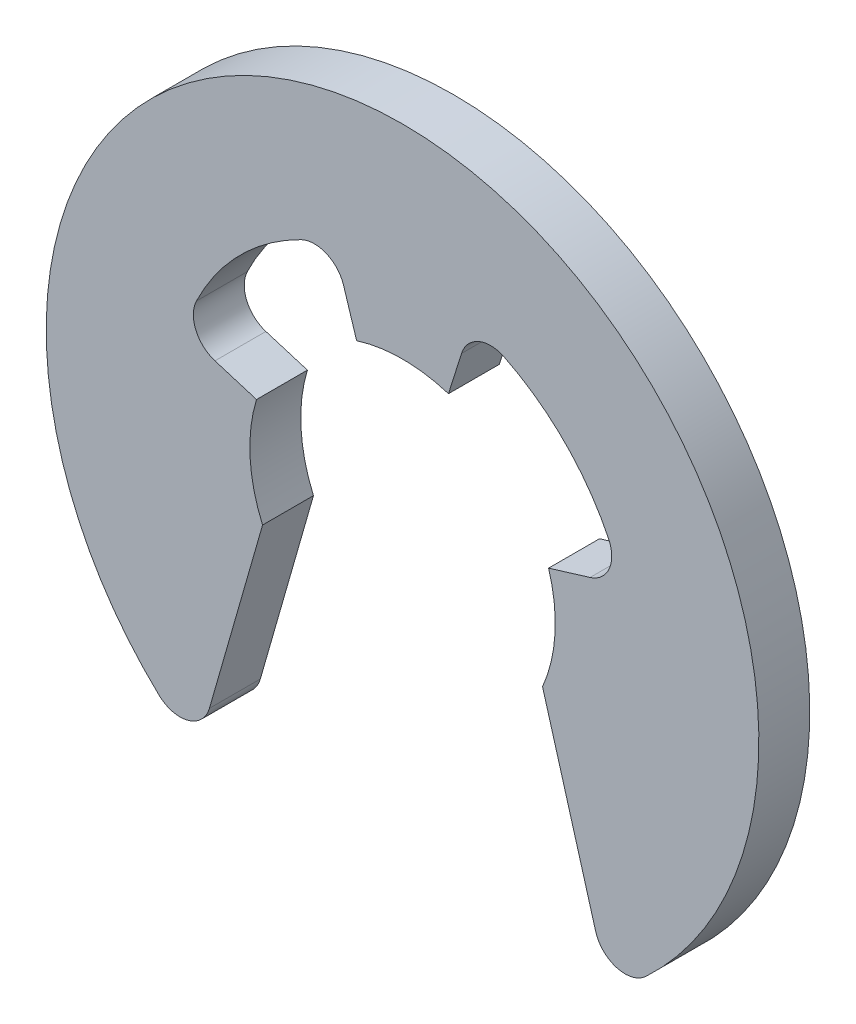
SolidWorks part; units mm, degrees
ref_plane "前视基准面" through (0, 0, 0) normal (0, 0, 1) x (1, 0, 0)
ref_plane "上视基准面" through (0, 0, 0) normal (0, 1, 0) x (1, 0, 0)
ref_plane "右视基准面" through (0, 0, 0) normal (1, 0, 0) x (0, 0, -1)
sketch "草图1" plane through (0, 0, 0) normal (0, 0, 1) x (1, 0, 0)
  line L0 (0, 0) -> (4.4829, 0.3922) construction
  line L1 (-2.193, 0) -> (1.9152, 0) construction
  line L2 (0, -1.8051) -> (0, 1.7867) construction
  line L3 (2.75, -1.199) -> (3.7941, -4.8403)
  line L4 (-2.75, -1.199) -> (-3.7941, -4.8403)
  line L5 (0.9021, 2.8612) -> (1.1588, 3.6752)
  line L6 (-0.9021, 2.8612) -> (-1.1588, 3.6752)
  line L7 (0, 0) -> (0.9021, 2.8612) construction
  line L8 (0.9021, 2.8612) -> (0, 0) construction
  line L9 (0, 0) -> (-0.9021, 2.8612) construction
  line L10 (2.8689, 0.8771) -> (3.6852, 1.1267)
  line L11 (-2.8689, 0.8771) -> (-3.6852, 1.1267)
  line L12 (0, 0) -> (2.8689, 0.8771) construction
  line L13 (2.8689, 0.8771) -> (0, 0) construction
  line L14 (0, 0) -> (-2.8689, 0.8771) construction
  arc A0 (2.75, -1.199) -> (2.8689, 0.8771) centre (0, 0) ccw
  arc A1 (4.5, 0) -> (4.4829, 0.3922) centre (0, 0) ccw
  arc A2 (4.7807, -5.1132) -> (-4.7807, -5.1132) centre (0, 0) ccw
  arc A3 (-1.9973, 4.0325) -> (-4.0497, 1.9621) centre (0, 0) ccw
  arc A4 (-2.8689, 0.8771) -> (-2.75, -1.199) centre (0, 0) ccw
  arc A5 (0.9021, 2.8612) -> (-0.9021, 2.8612) centre (0, 0) ccw
  arc A6 (4.0497, 1.9621) -> (1.9973, 4.0325) centre (0, 0) ccw
  arc A7 (-3.7941, -4.8403) -> (-4.7807, -5.1132) centre (-4.3709, -4.675) cw
  arc A8 (4.7807, -5.1132) -> (3.7941, -4.8403) centre (4.3709, -4.675) cw
  arc A9 (-4.0497, 1.9621) -> (-3.6852, 1.1267) centre (-3.5098, 1.7005) ccw
  arc A10 (-1.1588, 3.6752) -> (-1.9973, 4.0325) centre (-1.731, 3.4948) ccw
  arc A11 (1.9973, 4.0325) -> (1.1588, 3.6752) centre (1.731, 3.4948) ccw
  arc A12 (4.0497, 1.9621) -> (3.6852, 1.1267) centre (3.5098, 1.7005) cw
  point P22 (-4.0445, -5.7133)
  point P25 (4.0445, -5.7133)
  point P30 (-1.3532, 4.2917)
  point P33 (1.3532, 4.2917)
  point P36 (4.3034, 1.3157)
  dimension "D1" = 5
  dimension "d" = 6
  dimension "D3" = 17
  dimension "DD" = 14
  dimension "r" = 0.6
  dimension "D2" = 35
  dimension "RR" = 4.5
  dimension "D4" = 17
  dimension "angle" = 16
  dimension "B" = 5.5
extrude "拉伸1" add sketch "草图1" along normal blind 1
